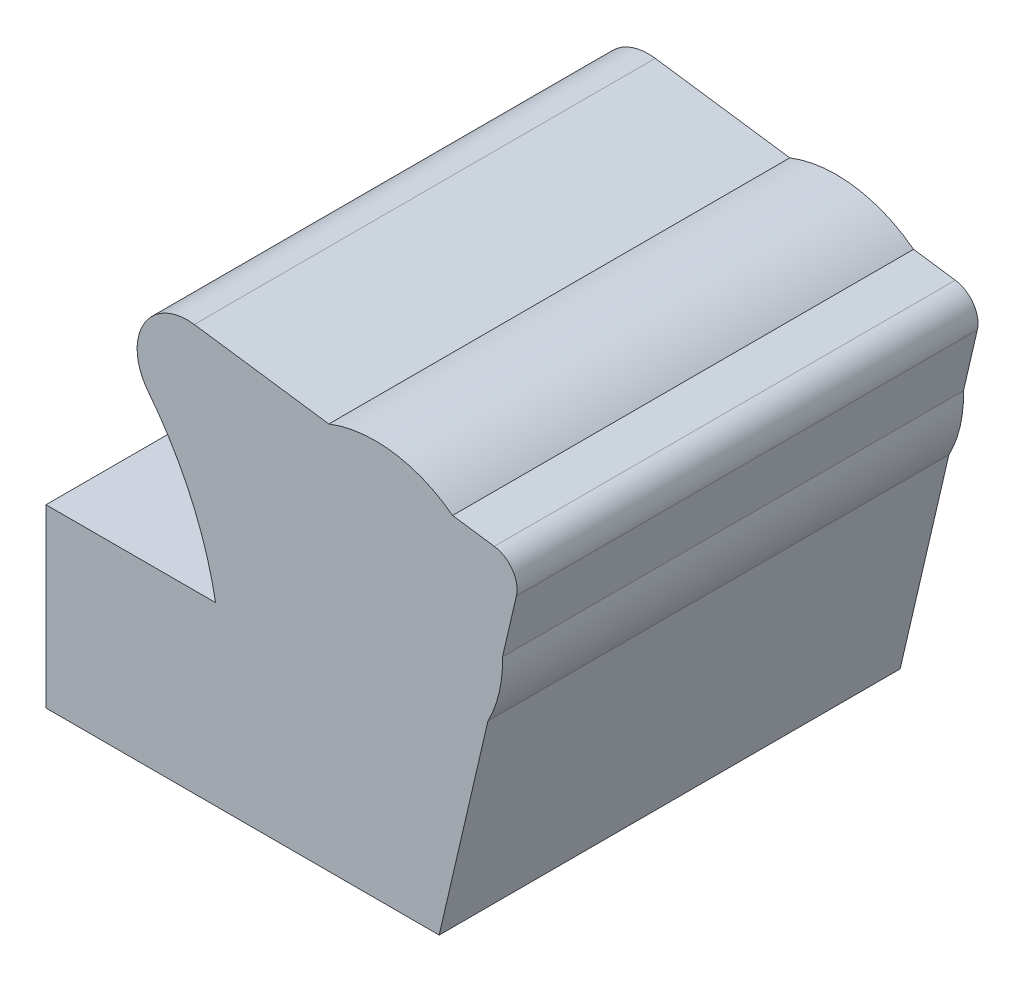
SolidWorks part; units mm, degrees
ref_plane "前视基准面" through (0, 0, 0) normal (0, 0, 1) x (1, 0, 0)
ref_plane "上视基准面" through (0, 0, 0) normal (0, 1, 0) x (1, 0, 0)
ref_plane "右视基准面" through (0, 0, 0) normal (1, 0, 0) x (0, 0, -1)
sketch "草图1" plane through (0, 0, 0) normal (0, 0, 1) x (1, 0, 0)
  line L1 (0, 29.5569) -> (33.8411, 29.5569)
  line L2 (116.7701, 26.4939) -> (125.1562, 47.9624)
  line L3 (152.6611, 126.9774) -> (87.5697, 136.1142)
  line L6 (86.0571, 125.3383) -> (126.841, 106.3205)
  line L8 (0, 0) -> (0, 29.5569)
  line L9 (33.8411, 29.5569) -> (55.4044, 43.1338)
  line L11 (144.001, 0) -> (133.5423, 26.4939)
  line L14 (89.661, -18.3061) -> (89.661, 35.0616) construction
  line L17 (125.1562, 47.9624) -> (140.6985, 47.9624)
  line L18 (140.6985, 47.9624) -> (157.4376, 120.0186)
  line L20 (133.5423, 26.4939) -> (116.7701, 26.4939)
  line L21 (55.4044, 43.1338) -> (55.4044, 86.1673)
  line L22 (0, 0) -> (144.001, 0)
  line L23 (55.4044, 86.1673) -> (92.2029, 86.1673)
  arc A2 (77.5087, 118.6055) -> (92.2029, 86.1673) centre (19.0918, 72.596) cw
  arc A9 (87.5697, 136.1142) -> (77.5087, 118.6055) centre (86.0571, 125.3383) ccw
  arc A10 (157.4376, 120.0186) -> (152.6611, 126.9774) centre (151.866, 121.3129) ccw
  circle A15 centre (126.841, 106.3205) radius 27.6011
  dimension "D2" = 55.2022
  dimension "D3" = 74.36
  dimension "D5" = 5.72
  dimension "D1" = 106.3205
  dimension "D6" = 19.0918
  dimension "D7" = 33.8411
  dimension "D8" = 55.4044
  dimension "D9" = 25
  dimension "D10" = 87.5697
  dimension "D11" = 89.661
  dimension "D12" = 151.866
  dimension "D13" = 92.2029
  dimension "D14" = 116.7701
  dimension "D15" = 125.1562
  dimension "D16" = 126.841
  dimension "D17" = 133.5423
  dimension "D18" = 140.6985
  dimension "D19" = 144.001
  dimension "D20" = 26.4939
  dimension "D21" = 29.5569
  dimension "D22" = 157.4376
  dimension "D23" = 43.1338
  dimension "D24" = 47.9624
  dimension "D25" = 45
extrude "凸台-拉伸1" add sketch "草图1" along normal mid plane 100
sketch "草图2" plane through (0, 0, 50) normal (0, 0, 1) x (1, 0, 0)
  line L0 (125.1562, 47.9624) -> (37.9215, 47.9624)
split "分割1" trim tools "草图2" bodies to split 106 resulting bodies 107 108
delete or keep bodies "实体-删除/保留 1" type keep bodies bodies 107
